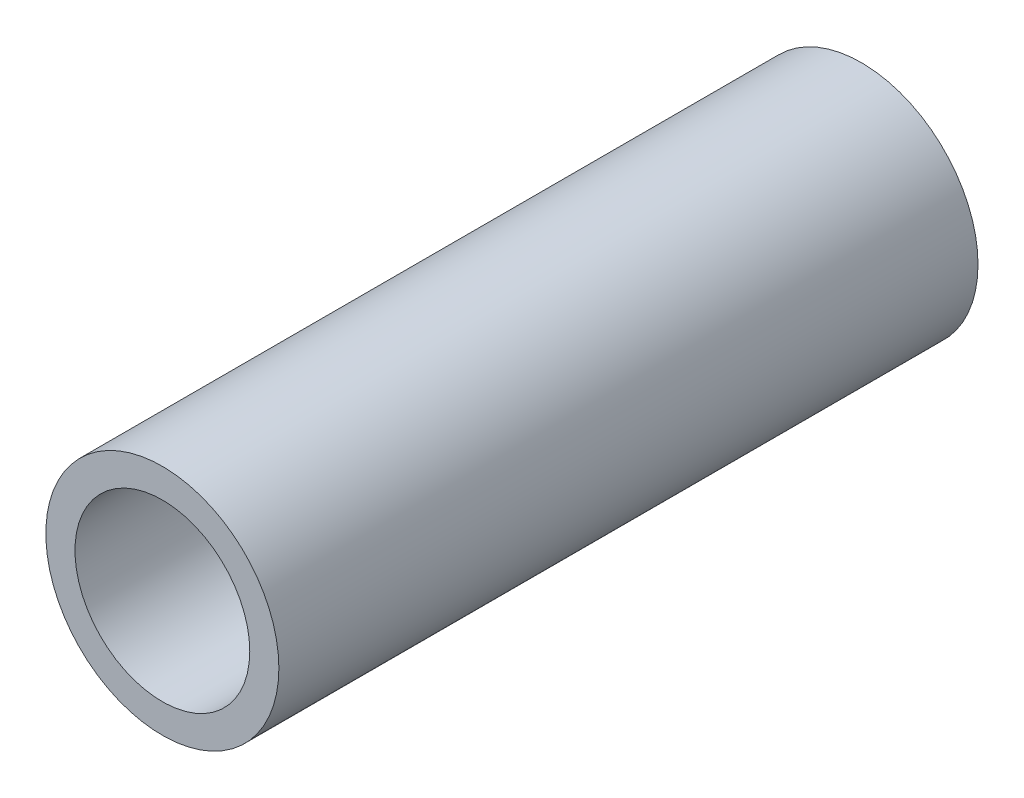
SolidWorks part; units mm, degrees
ref_plane "Front Plane" through (0, 0, 0) normal (0, 0, 1) x (1, 0, 0)
ref_plane "Top Plane" through (0, 0, 0) normal (0, 1, 0) x (1, 0, 0)
ref_plane "Right Plane" through (0, 0, 0) normal (1, 0, 0) x (0, 0, -1)
sketch "Sketch1" plane through (0, 0, 0) normal (0, 0, 1) x (1, 0, 0)
  circle A0 centre (0, 0) radius 3.175
  circle A1 centre (0, 0) radius 4.2333
  dimension "D1" = 6.35
  dimension "D2" = 8.4667
extrude "Boss-Extrude1" add sketch "Sketch1" along normal blind 25.4
